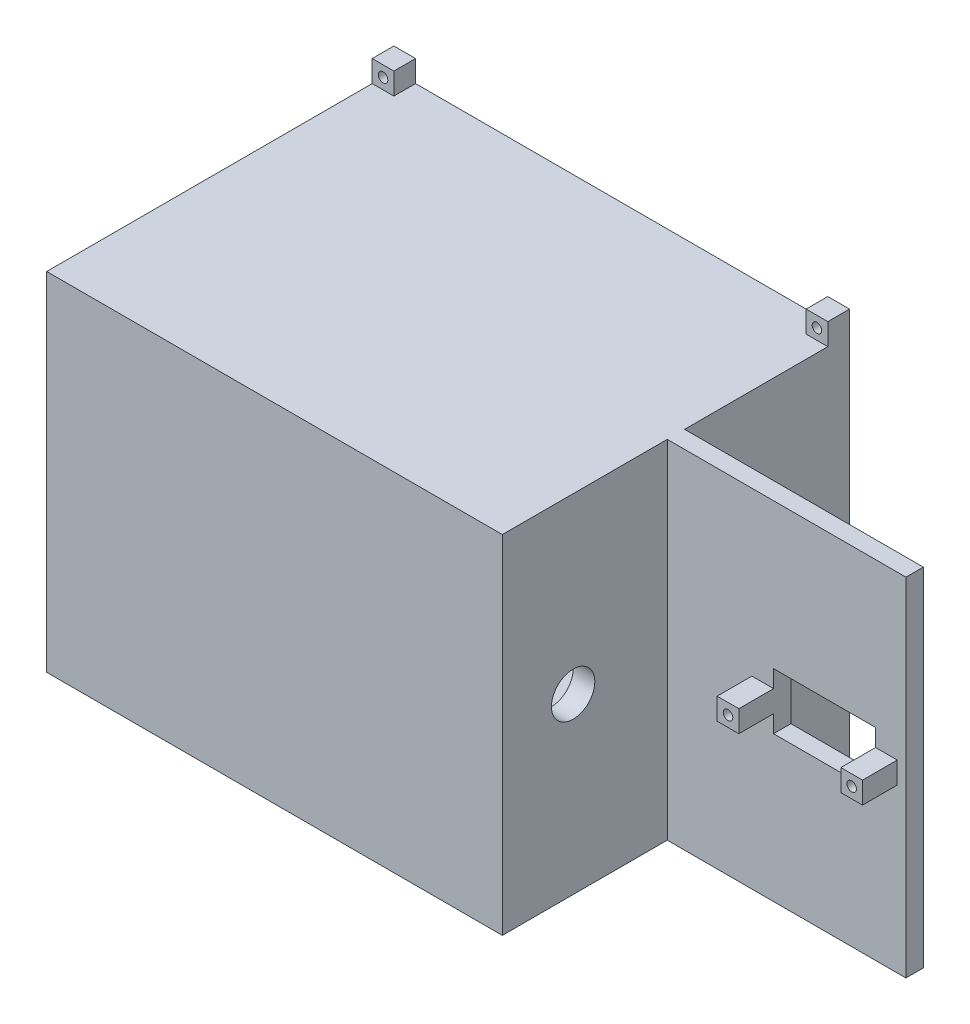
SolidWorks part; units mm, degrees
ref_plane "前基準面" through (0, 0, 0) normal (0, 0, 1) x (1, 0, 0)
ref_plane "上基準面" through (0, 0, 0) normal (0, 1, 0) x (1, 0, 0)
ref_plane "右基準面" through (0, 0, 0) normal (1, 0, 0) x (0, 0, -1)
sketch "草圖1" plane through (0, 0, 0) normal (0, 0, 1) x (1, 0, 0)
  line L0 (-75.5089, 45.5899) -> (84.4911, 45.5899)
  line L4 (-75.5089, 5.5899) -> (84.4911, 5.5899) construction
  line L5 (-75.5089, 45.5899) -> (-75.5089, -34.4101)
  line L6 (84.4911, 45.5899) -> (84.4911, -34.4101)
  line L7 (-75.5089, -34.4101) -> (84.4911, -34.4101)
  dimension "D1" = 160
  dimension "D2" = 80
extrude "填料-伸長1" add sketch "草圖1" along normal blind 80
sketch "草圖5" plane through (0, -34.4101, 0) normal (0, -1, 0) x (1, 0, 0)
  line L0 (39.4911, 80) -> (39.4911, 0)
  line L1 (-75.5089, 80) -> (84.4911, 80) construction
  line L2 (-75.5089, 0) -> (84.4911, 0) construction
  line L3 (39.4911, 0) -> (84.4911, 0)
  line L4 (84.4911, 0) -> (84.4911, 80)
  line L5 (84.4911, 80) -> (39.4911, 80)
  dimension "D1" = 45
ref_plane "平面2" through (0, -34.4101, 0) normal (0, -1, 0) x (-1, 0, 0)
sketch "草圖10" plane through (0, -34.4101, 0) normal (0, -1, 0) x (-1, 0, 0)
  line L0 (75.5089, 0) -> (-84.4911, 0) construction
  line L1 (14.0089, -15) -> (35.5089, -15)
  line L2 (14.0089, -15) -> (14.0089, -30)
  line L3 (14.0089, -30) -> (35.5089, -30)
  line L4 (35.5089, -15) -> (35.5089, -30)
  line L5 (75.5089, -80) -> (75.5089, 0) construction
  point P6 (24.7589, -15)
  dimension "D1" = 21.5
  dimension "D2" = 15
  dimension "D3" = 15
  dimension "D4" = 40
extrude "除料-伸長6" cut sketch "草圖10" against normal blind 10
ref_plane "平面3" through (0, 0, 0) normal (0, 0, -1) x (-1, 0, 0)
sketch "草圖11" plane through (0, 0, 0) normal (0, 0, -1) x (-1, 0, 0)
  line L0 (-84.4911, -34.4101) -> (-39.4911, -34.4101) construction
  line L1 (-84.4911, 45.5899) -> (-29.4911, 45.5899)
  line L2 (-84.4911, 45.5899) -> (-84.4911, -34.4101)
  line L3 (-84.4911, -34.4101) -> (-29.4911, -34.4101)
  line L4 (-29.4911, 45.5899) -> (-29.4911, -34.4101)
  dimension "D1" = 55
extrude "除料-伸長7" cut sketch "草圖11" against normal blind 38
ref_plane "平面4" through (0, 0, 80) normal (0, 0, 1) x (1, 0, 0)
sketch "草圖12" plane through (0, 0, 80) normal (0, 0, 1) x (1, 0, 0)
  line L0 (84.4911, -34.4101) -> (39.4911, -34.4101) construction
  line L1 (29.4911, -34.4101) -> (84.4911, -34.4101)
  line L2 (29.4911, -34.4101) -> (29.4911, 45.5899)
  line L3 (29.4911, 45.5899) -> (84.4911, 45.5899)
  line L4 (84.4911, -34.4101) -> (84.4911, 45.5899)
  dimension "D1" = 55
extrude "除料-伸長8" cut sketch "草圖12" against normal blind 38
sketch "草圖14" plane through (0, 0, 0) normal (0, 0, -1) x (-1, 0, 0)
  line L0 (-29.4911, -34.4101) -> (-29.4911, 45.5899) construction
  line L1 (-24.4911, 40.5899) -> (70.5089, 40.5899)
  line L2 (-24.4911, 40.5899) -> (-24.4911, -29.4101)
  line L3 (-24.4911, -29.4101) -> (70.5089, -29.4101)
  line L4 (70.5089, 40.5899) -> (70.5089, -29.4101)
  line L5 (-29.4911, 45.5899) -> (75.5089, 45.5899) construction
  line L6 (75.5089, 45.5899) -> (75.5089, -34.4101) construction
  line L7 (-44, -34.4101) -> (44, -34.4101) construction
  dimension "D1" = 5
  dimension "D2" = 5
  dimension "D3" = 5
  dimension "D4" = 5
extrude "除料-伸長9" cut sketch "草圖14" against normal blind 75
sketch "草圖15" plane through (0, 0, 0) normal (0, 0, -1) x (-1, 0, 0)
  line L0 (-29.4911, 5.5899) -> (-28.3911, 5.5899) construction
  line L1 (-29.4911, -34.4101) -> (-29.4911, 45.5899) construction
  line L2 (75.5089, 45.5899) -> (75.5089, -34.4101) construction
  line L3 (-28.3911, -33.3101) -> (-28.3911, 44.4899)
  line L4 (-28.3911, 44.4899) -> (74.4089, 44.4899)
  line L5 (74.4089, 44.4899) -> (74.4089, -33.3101)
  line L7 (71.6089, -30.5101) -> (71.6089, 41.6899)
  line L8 (71.6089, 41.6899) -> (-25.5911, 41.6899)
  line L9 (-25.5911, 41.6899) -> (-25.5911, -30.5101)
  line L11 (70.5089, -29.4101) -> (70.5089, 40.5899) construction
  line L12 (-29.4911, -34.4101) -> (-29.4911, 45.5899) construction
  line L13 (-29.4911, 45.5899) -> (75.5089, 45.5899) construction
  line L14 (71.6089, -30.5101) -> (-25.5911, -30.5101)
  line L15 (-28.3911, -33.3101) -> (74.4089, -33.3101)
  line L16 (-25.5911, 5.5899) -> (71.6089, 5.5899) construction
  line L17 (74.4089, 5.5899) -> (75.5089, 5.5899) construction
  dimension "D1" = 2.8
  dimension "D2" = 2.8
  dimension "D3" = 2.8
  dimension "D4" = 1.1
  dimension "D5" = 1.1
  dimension "D6" = 1.1
extrude "除料-伸長10" cut sketch "草圖15" against normal blind 10
sketch "草圖16" plane through (0, 0, 0) normal (0, 0, -1) x (-1, 0, 0)
  line L0 (-29.4911, 5.5899) -> (75.5089, 5.5899) construction
  line L1 (-29.4911, -34.4101) -> (-29.4911, 45.5899) construction
  line L2 (75.5089, 45.5899) -> (75.5089, -34.4101) construction
  line L3 (23.0089, 45.5899) -> (23.0089, -34.4101) construction
  line L4 (-29.4911, 45.5899) -> (75.5089, 45.5899) construction
  line L5 (-44, -34.4101) -> (44, -34.4101) construction
  line L6 (-29.4911, 48.0899) -> (-24.4911, 48.0899) construction
  line L7 (-29.4911, 45.5899) -> (-24.4911, 45.5899)
  line L8 (-29.4911, 45.5899) -> (-29.4911, 50.5899)
  line L9 (-29.4911, 50.5899) -> (-24.4911, 50.5899)
  line L10 (-24.4911, 45.5899) -> (-24.4911, 50.5899)
  line L11 (-26.9911, 50.5899) -> (-26.9911, 45.5899) construction
  line L12 (75.5089, 50.5899) -> (70.5089, 50.5899)
  line L13 (70.5089, 45.5899) -> (70.5089, 50.5899)
  line L14 (75.5089, 45.5899) -> (70.5089, 45.5899)
  line L15 (75.5089, 45.5899) -> (75.5089, 50.5899)
  line L16 (75.5089, -34.4101) -> (75.5089, -39.4101)
  line L17 (75.5089, -34.4101) -> (70.5089, -34.4101)
  line L18 (70.5089, -34.4101) -> (70.5089, -39.4101)
  line L19 (75.5089, -39.4101) -> (70.5089, -39.4101)
  line L20 (-29.4911, -39.4101) -> (-24.4911, -39.4101)
  line L21 (-24.4911, -34.4101) -> (-24.4911, -39.4101)
  line L22 (-29.4911, -34.4101) -> (-24.4911, -34.4101)
  line L23 (-29.4911, -34.4101) -> (-29.4911, -39.4101)
  circle A0 centre (-26.9911, 48.0899) radius 1.1
  circle A1 centre (73.0089, 48.0899) radius 1.1
  circle A2 centre (73.0089, -36.9101) radius 1.1
  circle A3 centre (-26.9911, -36.9101) radius 1.1
  dimension "D3" = 2.2
  dimension "D1" = 5
  dimension "D2" = 5
extrude "填料-伸長2" add sketch "草圖16" against normal blind 5
ref_plane "平面5" through (29.4911, 0, 0) normal (1, 0, 0) x (0, 0, -1)
sketch "草圖17" plane through (29.4911, 0, 0) normal (1, 0, 0) x (0, 0, -1)
  line L0 (-40, 45.5899) -> (-40, -34.4101) construction
  line L1 (-42, 45.5899) -> (-38, 45.5899) construction
  line L2 (-80, -34.4101) -> (0, -34.4101) construction
  line L3 (0, 5.5899) -> (-80, 5.5899) construction
  line L4 (0, -39.4101) -> (0, 50.5899) construction
  line L5 (-80, 44) -> (-80, -44) construction
  circle A0 centre (-63.6917, 5.5899) radius 5
  circle A1 centre (-16.3083, 5.5899) radius 5
  dimension "D1" = 10
extrude "除料-伸長12" cut sketch "草圖17" against normal blind 9.2
ref_plane "平面6" through (0, 0, 38) normal (0, 0, -1) x (-1, 0, 0)
sketch "草圖18" plane through (0, 0, 38) normal (0, 0, -1) x (-1, 0, 0)
  line L0 (-84.4911, 5.5899) -> (-29.4911, 5.5899) construction
  line L1 (-84.4911, 45.5899) -> (-84.4911, -34.4101) construction
  line L2 (-29.4911, 46.4331) -> (-29.4911, -46.4331) construction
  line L4 (-77.4911, 12.0899) -> (-53.9911, 12.0899)
  line L5 (-77.4911, 12.0899) -> (-77.4911, -0.9101)
  line L6 (-77.4911, -0.9101) -> (-53.9911, -0.9101)
  line L7 (-53.9911, 12.0899) -> (-53.9911, -0.9101)
  dimension "D1" = 13
  dimension "D2" = 6.5
  dimension "D3" = 23.5
  dimension "D4" = 7
extrude "除料-伸長13" cut sketch "草圖18" against normal blind 9.2
sketch "草圖19" plane through (0, 0, 38) normal (0, 0, -1) x (-1, 0, 0)
  line L0 (-84.4911, 5.5899) -> (-28.3911, 5.5899) construction
  line L1 (-84.4911, 45.5899) -> (-84.4911, -34.4101) construction
  line L2 (-28.3911, 44.4899) -> (-28.3911, -33.3101) construction
  line L3 (-77.4911, 12.0899) -> (-77.4911, -0.9101) construction
  line L4 (-82.4911, 8.0899) -> (-77.4911, 8.0899)
  line L5 (-82.4911, 8.0899) -> (-82.4911, 3.0899)
  line L6 (-82.4911, 3.0899) -> (-77.4911, 3.0899)
  line L7 (-77.4911, 8.0899) -> (-77.4911, 3.0899)
  line L8 (-53.9911, -0.9101) -> (-53.9911, 12.0899) construction
  line L9 (-53.9911, 8.0899) -> (-48.9911, 8.0899)
  line L10 (-53.9911, 8.0899) -> (-53.9911, 3.0899)
  line L11 (-53.9911, 3.0899) -> (-48.9911, 3.0899)
  line L12 (-48.9911, 8.0899) -> (-48.9911, 3.0899)
  line L13 (-79.9911, 8.0899) -> (-79.9911, 3.0899) construction
  line L14 (-51.4911, 8.0899) -> (-51.4911, 3.0899) construction
  circle A0 centre (-79.9911, 5.5899) radius 1.1
  circle A1 centre (-51.4911, 5.5899) radius 1.1
  dimension "D7" = 2.2
  dimension "D8" = 2.2
  dimension "D1" = 5
  dimension "D2" = 5
  dimension "D3" = 2.5
  dimension "D4" = 2.5
  dimension "D5" = 5
  dimension "D6" = 5
extrude "填料-伸長3" add sketch "草圖19" against normal blind 12
sketch "草圖20" plane through (0, 0, 38) normal (0, 0, -1) x (-1, 0, 0)
  line L0 (-79.9911, 8.0899) -> (-79.9911, 3.0899) construction
  circle A0 centre (-79.9911, 5.5899) radius 1.1
  circle A1 centre (-51.4911, 5.5899) radius 1.1
extrude "除料-伸長14" cut sketch "草圖20" against normal blind 5 and the other way blind 5
